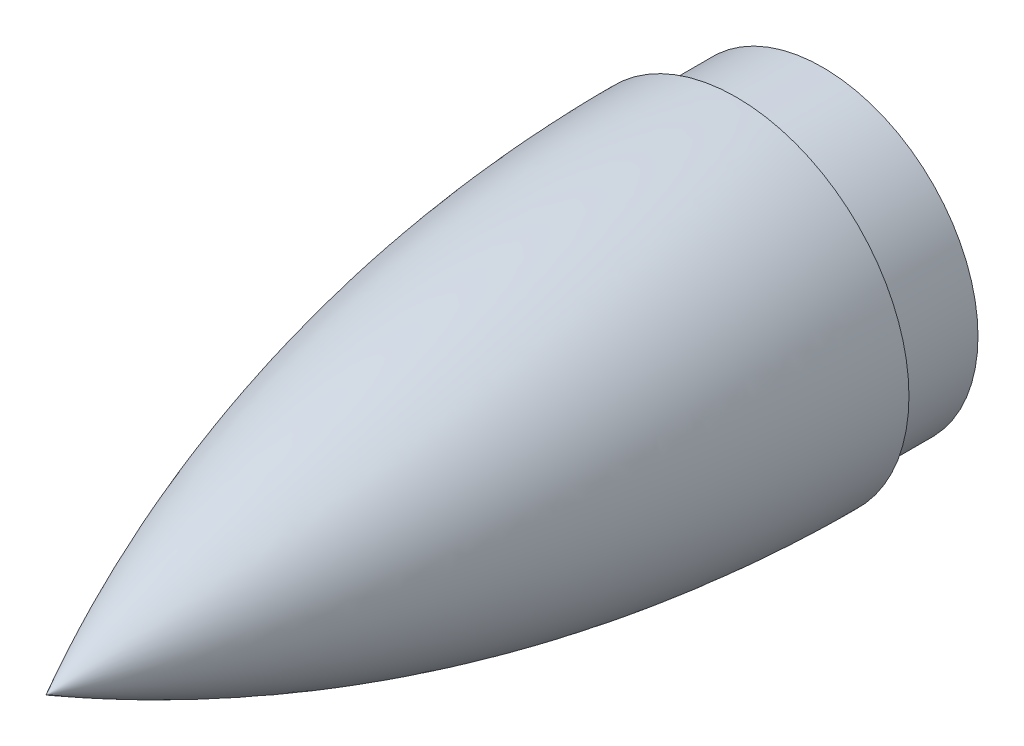
SolidWorks part; units mm, degrees
ref_plane "Front Plane" through (0, 0, 0) normal (0, 0, 1) x (1, 0, 0)
ref_plane "Top Plane" through (0, 0, 0) normal (0, 1, 0) x (1, 0, 0)
ref_plane "Right Plane" through (0, 0, 0) normal (1, 0, 0) x (0, 0, -1)
sketch "Sketch2" plane through (0, 0, 0) normal (1, 0, 0) x (0, 0, -1)
  line L0 (0, 0) -> (94.1416, 0) construction
  line L1 (80, 20) -> (80, 18)
  line L2 (80, 18) -> (90, 18)
  line L3 (90, 18) -> (90, 0)
  line L4 (90, 0) -> (0, 0)
  spline S0 degree 8 poles (-7.2249, -4.0828) (4.6782, 3.0323) (16.5814, 8.642) (28.4845, 13.0371) (40.3876, 16.3401) (52.2907, 18.64) (64.1938, 19.9773) (76.0969, 20.3725) (88, 19.8116) knots 0 0 0 0 0 0 0 0 0 1 1 1 1 1 1 1 1 1 construction
  spline S1 degree 8 poles (0, 0) (10, 5.3333) (20, 9.6881) (30, 13.2031) (40, 15.9513) (50, 17.9833) (60, 19.3277) (70, 20) (80, 20) knots 0.075872 0.075872 0.075872 0.075872 0.075872 0.075872 0.075872 0.075872 0.075872 0.915988 0.915988 0.915988 0.915988 0.915988 0.915988 0.915988 0.915988 0.915988
  dimension "D1" = 80
  dimension "D2" = 10
  dimension "D3" = 18
revolve "Revolve1" add sketch "Sketch2" angle 360 about L0
